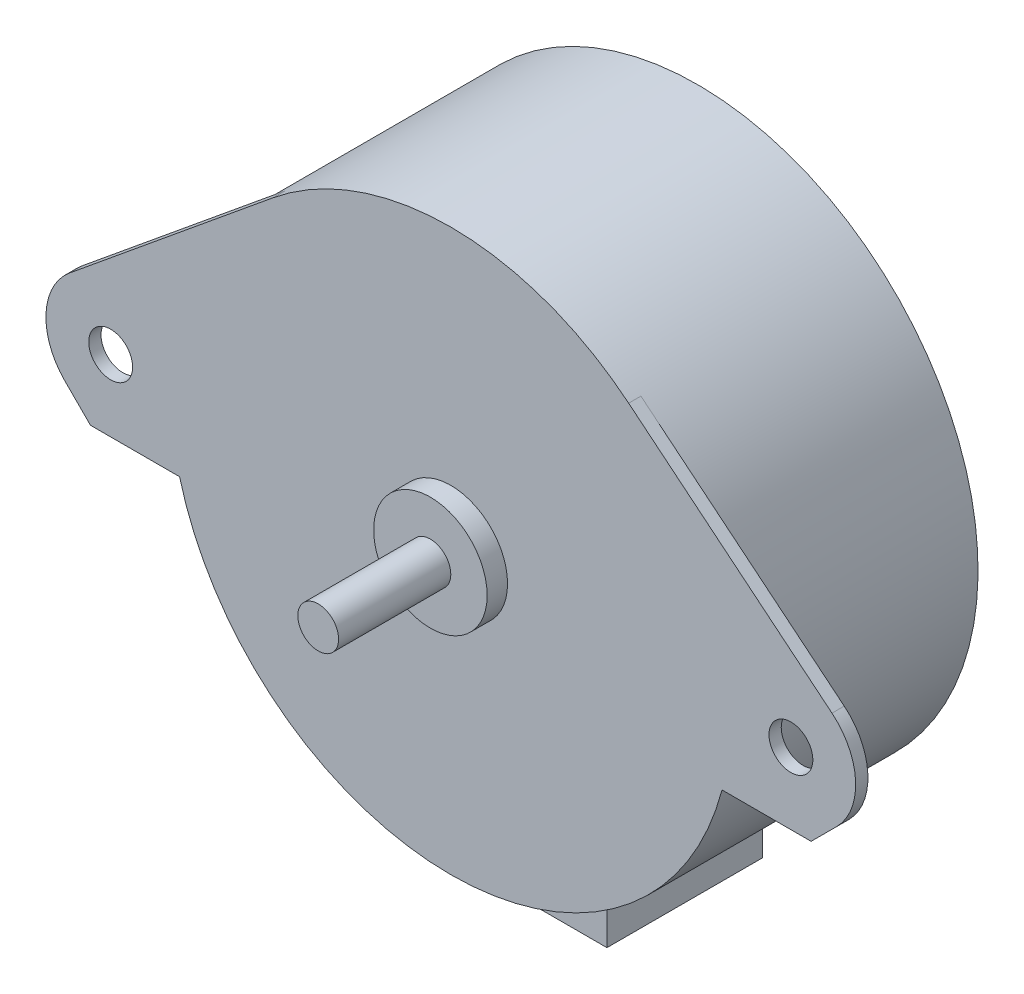
SolidWorks part; units mm, degrees
ref_plane "Front Plane" through (0, 0, 0) normal (0, 0, 1) x (1, 0, 0)
ref_plane "Top Plane" through (0, 0, 0) normal (0, 1, 0) x (1, 0, 0)
ref_plane "Right Plane" through (0, 0, 0) normal (1, 0, 0) x (0, 0, -1)
sketch "Sketch1" plane through (0, 0, 0) normal (1, 0, 0) x (0, 0, -1)
  line L0 (0, 0) -> (0, 2)
  line L1 (0, 2) -> (-1, 2)
  line L2 (-1, 2) -> (-1, 27.5)
  line L3 (-1, 27.5) -> (-24, 27.5)
  line L4 (-24, 27.5) -> (-24, 5.565)
  line L5 (-24, 5.565) -> (-27.2, 5.565)
  line L6 (-27.2, 5.565) -> (-27.2, 2)
  line L7 (-27.2, 2) -> (-38.2, 2)
  line L8 (-38.2, 2) -> (-38.2, 0)
  line L9 (-38.2, 0) -> (0, 0)
  dimension "D1" = 2
  dimension "D2" = 27.5
  dimension "D3" = 1
  dimension "D4" = 23
  dimension "D5" = 3.2
  dimension "D6" = 14.2
  dimension "D7" = 5.565
revolve "Revolve1" add sketch "Sketch1" angle 360 about L9
sketch "Sketch2" plane through (0, 0, 24) normal (0, 0, 1) x (1, 0, 0)
  line L0 (-17.44, 21.2625) -> (-37.3771, 4.9097)
  line L1 (-37.8401, -4.4901) -> (-35.3303, -7)
  line L2 (-35.3303, -7) -> (-26.5942, -7)
  line L3 (-33.35, 0) -> (33.35, 0) construction
  line L4 (35.3303, -7) -> (26.5942, -7)
  line L5 (37.8401, -4.4901) -> (35.3303, -7)
  line L6 (17.44, 21.2625) -> (37.3771, 4.9097)
  circle A0 centre (0, 0) radius 27.5 construction
  arc A1 (-26.5942, -7) -> (26.5942, -7) centre (0, 0) ccw construction
  arc A2 (-26.5942, -7) -> (26.5942, -7) centre (0, 0) ccw
  arc A3 (-37.3771, 4.9097) -> (-37.8401, -4.4901) centre (-33.35, 0) ccw
  arc A4 (37.3771, 4.9097) -> (37.8401, -4.4901) centre (33.35, 0) cw
  circle A5 centre (-33.35, 0) radius 2.15
  circle A6 centre (33.35, 0) radius 2.15
  arc A7 (17.44, 21.2625) -> (-17.44, 21.2625) centre (0, 0) ccw construction
  arc A8 (17.44, 21.2625) -> (-17.44, 21.2625) centre (0, 0) ccw
  circle A10 centre (0, 0) radius 5.565 construction
  circle A11 centre (0, 0) radius 5.565
  point P3 (0, 0)
  dimension "D2" = 4.3
  dimension "D3" = 6.35
  dimension "D1" = 7
  dimension "D4" = 135
  dimension "D5" = 66.7
extrude "Boss-Extrude1" add sketch "Sketch2" along normal blind 1.2
sketch "Sketch3" plane through (0, 0, 0) normal (0, 1, 0) x (1, 0, 0)
  line L0 (27.5, -1) -> (-27.5, -1) construction
  line L1 (-6.35, -1) -> (6.35, -1)
  line L2 (-6.35, -1) -> (-6.35, -16.24)
  line L3 (-6.35, -16.24) -> (6.35, -16.24)
  line L4 (6.35, -1) -> (6.35, -16.24)
  line L5 (0, -38.2) -> (0, -1) construction
  line L6 (-2, -38.2) -> (2, -38.2) construction
  dimension "D1" = 12.7
  dimension "D2" = 15.24
extrude "Boss-Extrude2" add sketch "Sketch3" against normal blind 35
